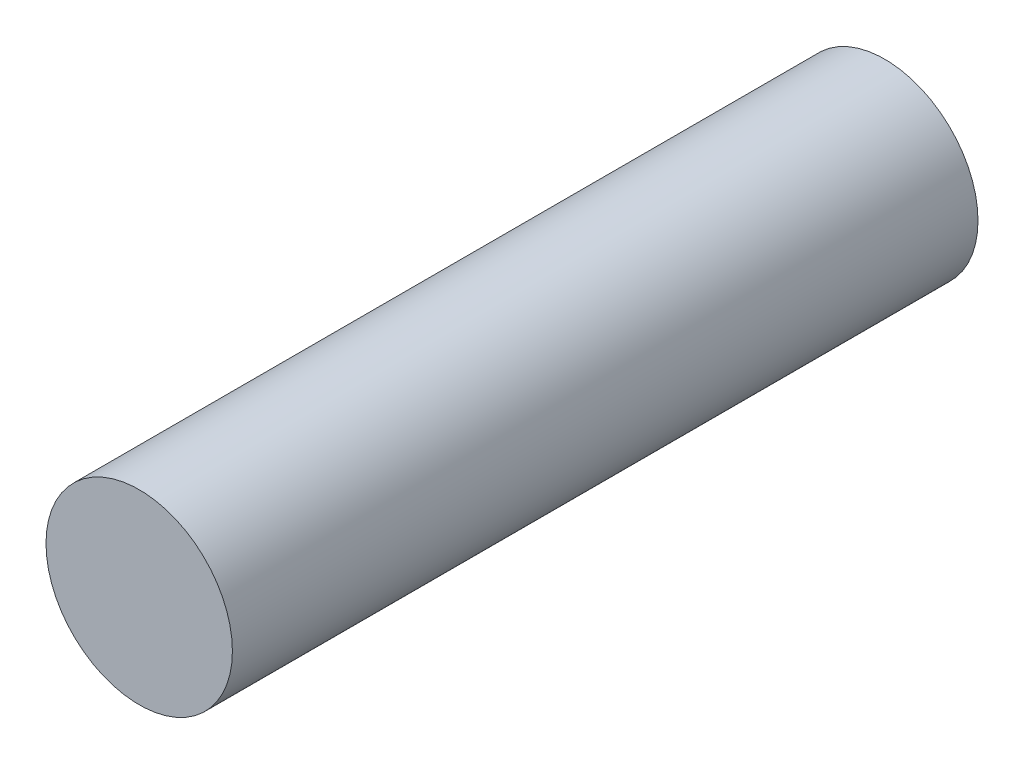
SolidWorks part; units mm, degrees
material "ASTM A36 Steel"
ref_plane "Front Plane" through (0, 0, 0) normal (0, 0, 1) x (1, 0, 0)
ref_plane "Top Plane" through (0, 0, 0) normal (0, 1, 0) x (1, 0, 0)
ref_plane "Right Plane" through (0, 0, 0) normal (1, 0, 0) x (0, 0, -1)
sketch "Sketch1" plane through (0, 0, 0) normal (0, 0, 1) x (1, 0, 0)
  circle A0 centre (0, 0) radius 3.175
  dimension "D1" = 6.35
extrude "Boss-Extrude1" add sketch "Sketch1" along normal blind 25.4
